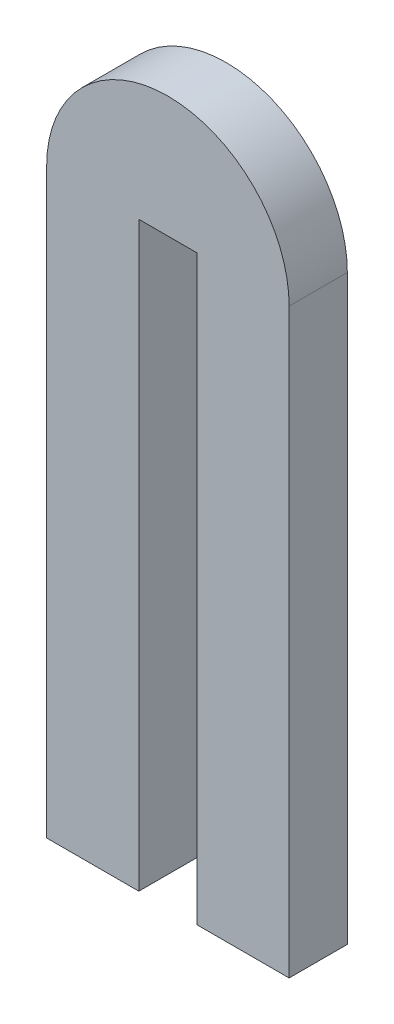
SolidWorks part; units mm, degrees
ref_plane "Front Plane" through (0, 0, 0) normal (0, 0, 1) x (1, 0, 0)
ref_plane "Top Plane" through (0, 0, 0) normal (0, 1, 0) x (1, 0, 0)
ref_plane "Right Plane" through (0, 0, 0) normal (1, 0, 0) x (0, 0, -1)
sketch "Sketch1" plane through (0, 0, 0) normal (0, 0, 1) x (1, 0, 0)
  line L0 (1.5, -15) -> (6.25, -15)
  line L2 (-6.25, 15) -> (-6.25, -15)
  line L3 (-6.25, -15) -> (-1.5, -15)
  line L4 (6.25, 15) -> (6.25, -15)
  line L5 (-6.25, 15) -> (6.25, -15) construction
  line L6 (-6.25, -15) -> (6.25, 15) construction
  line L8 (-1.5, -15) -> (-1.5, 15)
  line L9 (-1.5, 15) -> (1.5, 15)
  line L10 (1.5, -15) -> (1.5, 15)
  arc A0 (6.25, 15) -> (-6.25, 15) centre (0, 15) ccw
  point P0 (0, 0)
  dimension "D2" = 12.5
  dimension "D1" = 12.5
  dimension "D3" = 30
  dimension "D4" = 30
  dimension "D5" = 4.75
  dimension "D6" = 4.75
extrude "Boss-Extrude1" add sketch "Sketch1" along normal mid plane 3
